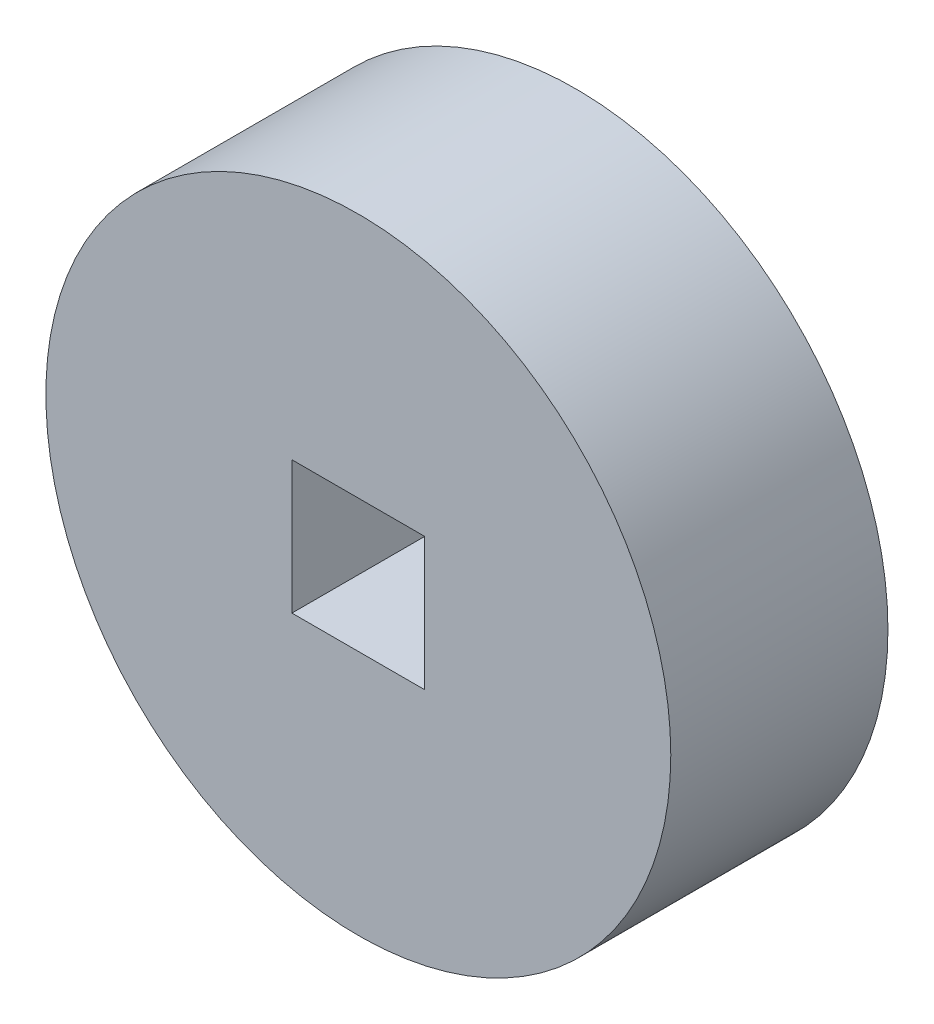
SolidWorks part; units mm, degrees
ref_plane "Ebene vorne" through (0, 0, 0) normal (0, 0, 1) x (1, 0, 0)
ref_plane "Ebene oben" through (0, 0, 0) normal (0, 1, 0) x (1, 0, 0)
ref_plane "Ebene rechts" through (0, 0, 0) normal (1, 0, 0) x (0, 0, -1)
sketch "Sketch1" plane through (0, 0, 0) normal (0, 0, 1) x (1, 0, 0)
  circle A0 centre (0, 0) radius 12
  dimension "D1" = 24
extrude "Boss-Extrude1" add sketch "Sketch1" against normal blind 8.34 from offset 8
sketch "Sketch3" plane through (0, 0, 0) normal (0, 0, 1) x (1, 0, 0)
  line L1 (-2.55, -2.55) -> (2.55, -2.55)
  line L2 (-2.55, -2.55) -> (-2.55, 2.55)
  line L3 (-2.55, 2.55) -> (2.55, 2.55)
  line L4 (2.55, -2.55) -> (2.55, 2.55)
  line L5 (-2.55, -2.55) -> (2.55, 2.55) construction
  line L6 (-2.55, 2.55) -> (2.55, -2.55) construction
  point P0 (0, 0)
  dimension "D1" = 5.1
  dimension "D2" = 5.1
extrude "Cut-Extrude4" cut sketch "Sketch3" along normal through all
